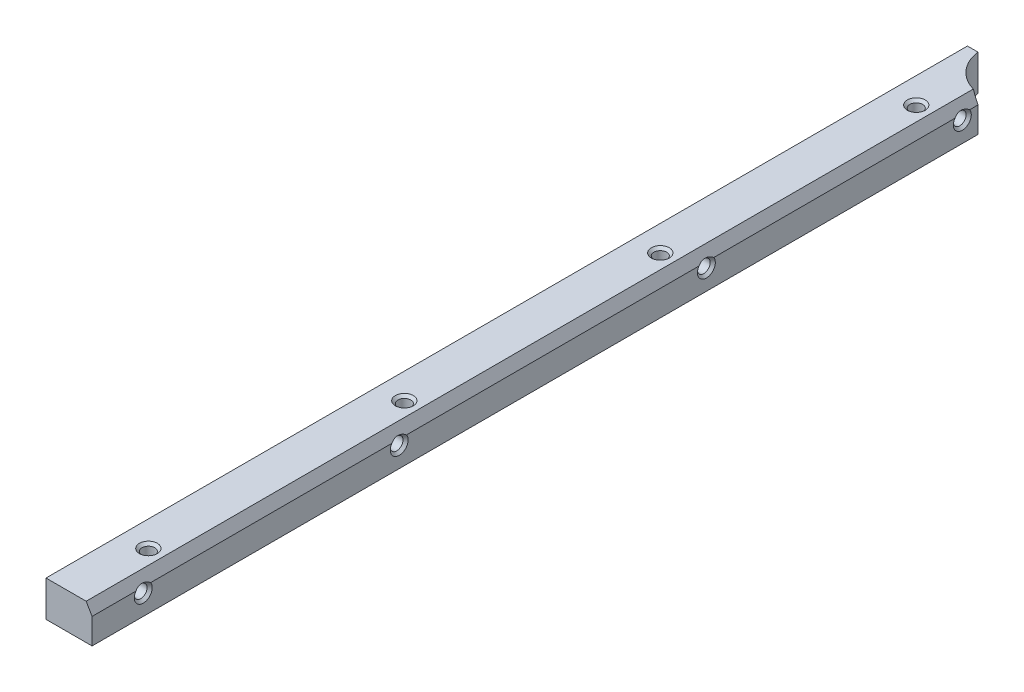
SolidWorks part; units mm, degrees
material "2024-T3"
ref_plane "Спереди" through (0, 0, 0) normal (0, 0, 1) x (1, 0, 0)
ref_plane "Сверху" through (0, 0, 0) normal (0, 1, 0) x (1, 0, 0)
ref_plane "Справа" through (0, 0, 0) normal (1, 0, 0) x (0, 0, -1)
sketch "Эскиз1" plane through (0, 0, 0) normal (0, 0, 1) x (1, 0, 0)
  line L1 (0, 0) -> (9, 0)
  line L2 (0, 0) -> (0, 7)
  line L3 (0, 7) -> (9, 7)
  line L4 (9, 0) -> (9, 7)
  dimension "D1" = 9
  dimension "D2" = 7
extrude "Бобышка-Вытянуть1" add sketch "Эскиз1" along normal blind 180
sketch "Эскиз6" plane through (0, 0, 0) normal (0, -1, 0) x (1, 0, 0)
  line L0 (0, 0) -> (9, 0) construction
  line L1 (9, 180) -> (9, 0) construction
  arc A0 (2.0627, 0) -> (9, 6.9373) centre (10, -1) cw
  dimension "D1" = 8
  dimension "D2" = 1
  dimension "D3" = 1
extrude "Вырез-Вытянуть1" cut sketch "Эскиз6" against normal through all and the other way through all flip side to cut
chamfer "Фаска1" distance 2 angle 30 1 edges at (9, 7, 93.4686)
hole_wizard "Отверстие обработанное метчиком M31" positions "Эскиз3" profile "Эскиз2" tap size "M3" standard "DIN" end condition through all
sketch "Эскиз3" plane through (0, 0, 0) normal (0, -1, 0) x (1, 0, 0)
  line L0 (0, 0) -> (2.0627, 0) construction
  line L1 (0, 180) -> (0, 0) construction
  point P0 (5, 15)
  point P1 (5, 65)
  point P3 (5, 115)
  point P5 (5, 165)
  dimension "D1" = 50
  dimension "D2" = 50
  dimension "D3" = 50
  dimension "D4" = 15
  dimension "D5" = 5
sketch "Эскиз2" plane through (5, 0, 15) normal (1, 0, 0) x (0, 0, -1)
  line L0 (0, 0) -> (0, 7)
  line L1 (0, 7) -> (1.75, 7)
  line L2 (1.25, 6.5) -> (1.25, 0.5)
  line L3 (1.25, 0.5) -> (1.75, 0)
  line L5 (1.75, 0) -> (0, 0)
  line L6 (-1.25, 0.5) -> (-1.75, 0) construction
  line L7 (1.75, 7) -> (1.25, 6.5)
  line L8 (-1.75, 7) -> (-1.25, 6.5) construction
  line L11 (0, -6.35) -> (0, 107.95) construction
  dimension "Диаметр проходного сверла" = 2.5
  dimension "Глубина проходного сверла" = 7
  dimension "Диаметр передней зенковки" = 3.5
  dimension "Угол передней зенковки" = 90
  dimension "Диаметр задней зенковки" = 3.5
  dimension "Угол задней зенковки" = 90
cosmetic thread "Отверстие резьбы1" parameters "D2"=3
cosmetic thread "Отверстие резьбы2" parameters "D2"=3
cosmetic thread "Отверстие резьбы3" parameters "D2"=3
cosmetic thread "Отверстие резьбы4" parameters "D2"=3
hole_wizard "Отверстие обработанное метчиком M32" positions "Эскиз5" profile "Эскиз4" tap size "M3" standard "DIN" end condition through all
sketch "Эскиз5" plane through (0, 0, 0) normal (-1, 0, 0) x (0, 0, 1)
  line L0 (0, 7) -> (0, 0) construction
  line L1 (180, 0) -> (0, 0) construction
  point P0 (10, 4)
  point P1 (60, 4)
  point P3 (120, 4)
  point P5 (170, 4)
  dimension "D1" = 50
  dimension "D2" = 60
  dimension "D3" = 50
  dimension "D4" = 10
  dimension "D5" = 4
sketch "Эскиз4" plane through (0, 4, 10) normal (0, 1, 0) x (0, 0, 1)
  line L0 (0, 0) -> (0, 9)
  line L1 (0, 9) -> (1.75, 9)
  line L2 (1.25, 8.5) -> (1.25, 0.5)
  line L3 (1.25, 0.5) -> (1.75, 0)
  line L5 (1.75, 0) -> (0, 0)
  line L6 (-1.25, 0.5) -> (-1.75, 0) construction
  line L7 (1.75, 9) -> (1.25, 8.5)
  line L8 (-1.75, 9) -> (-1.25, 8.5) construction
  line L11 (0, -6.35) -> (0, 107.95) construction
  dimension "Диаметр проходного сверла" = 2.5
  dimension "Глубина проходного сверла" = 9
  dimension "Диаметр передней зенковки" = 3.5
  dimension "Угол передней зенковки" = 90
  dimension "Диаметр задней зенковки" = 3.5
  dimension "Угол задней зенковки" = 90
cosmetic thread "Отверстие резьбы5" parameters "D2"=3
cosmetic thread "Отверстие резьбы6" parameters "D2"=3
cosmetic thread "Отверстие резьбы7" parameters "D2"=3
cosmetic thread "Отверстие резьбы8" parameters "D2"=3
